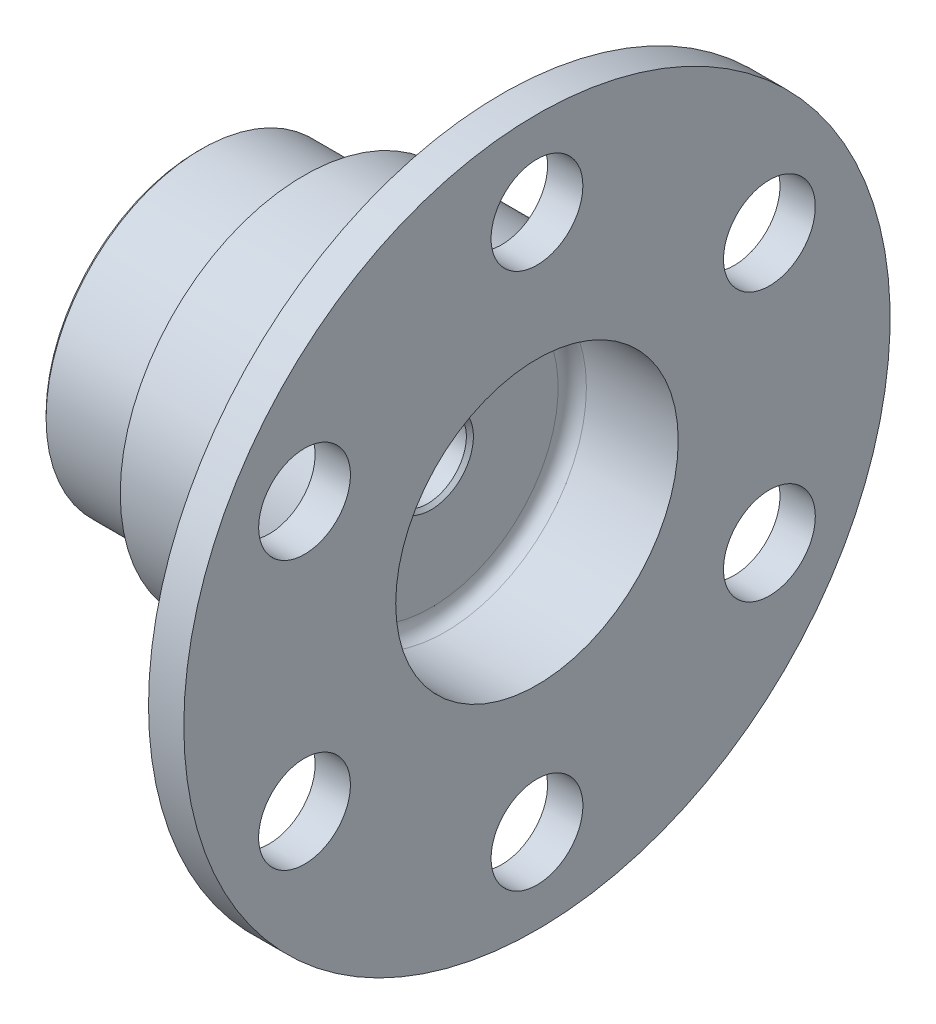
SolidWorks part; units mm, degrees
material "1.0035 (S185)"
ref_plane "Płaszczyzna przednia" through (0, 0, 0) normal (0, 0, 1) x (1, 0, 0)
ref_plane "Płaszczyzna górna" through (0, 0, 0) normal (0, 1, 0) x (1, 0, 0)
ref_plane "Płaszczyzna prawa" through (0, 0, 0) normal (1, 0, 0) x (0, 0, -1)
sketch "Szkic2" plane through (0, 0, 0) normal (0, 0, 1) x (1, 0, 0)
  line L0 (0, 0) -> (86.0541, 0) construction
  line L1 (0, 15.75) -> (29, 15.75)
  line L2 (29, 15.75) -> (29, 5.5)
  line L3 (29, 5.5) -> (33, 5.5)
  line L4 (33, 5.5) -> (33, 20)
  line L5 (33, 20) -> (48, 20)
  line L6 (48, 20) -> (48, 50)
  line L7 (48, 50) -> (43, 50)
  line L8 (43, 50) -> (43, 26)
  line L9 (43, 26) -> (15, 26)
  line L10 (0, 22) -> (0, 15.75)
  line L11 (0, 22) -> (15, 22)
  line L12 (15, 22) -> (15, 26)
  dimension "D1" = 11
  dimension "D2" = 31.5
  dimension "D3" = 5
  dimension "D4" = 4
  dimension "D5" = 29
  dimension "D6" = 100
  dimension "D7" = 52
  dimension "D8" = 15
  dimension "D9" = 40
  dimension "D10" = 15
  dimension "D11" = 44
revolve "Obrót1" add sketch "Szkic2" angle 360 about L0
sketch "Szkic4" plane through (48, 0, 0) normal (1, 0, 0) x (0, 0, -1)
  circle A0 centre (0, 38) radius 6.5
  dimension "D2" = 13
  dimension "D1" = 38
extrude "Wytnij-wyciągnięcie1" cut sketch "Szkic4" against normal blind 10
pattern_circular "Szyk kołowy1" count 6 over 360 about axis through (0, 0, 0) along (1, 0, 0) of "Wytnij-wyciągnięcie1"
fillet "Zaokrąglenie1" radius 2 2 edges at (43, 0, 26) (33, 0, 20)
sketch "Szkic6" plane through (29, 0, 0) normal (-1, 0, 0) x (0, 0, 1)
  line L0 (-4.3282, -14.981) -> (-4.3392, -15.181)
  line L1 (2.6503, -15.5649) -> (2.6612, -15.3649)
  line L2 (-12.1545, -10.0776) -> (-11.9758, -9.9872)
  line L3 (-4.1816, -15.1847) -> (-4.1926, -15.3847) construction
  line L4 (-15.138, -3.7421) -> (-15.3167, -3.8326)
  line L5 (-14.8047, 5.4873) -> (-14.637, 5.3777)
  line L6 (-10.8098, 11.2388) -> (-10.9775, 11.3483)
  line L7 (-2.6503, 15.5649) -> (-2.6612, 15.3649)
  line L8 (4.3282, 14.981) -> (4.3392, 15.181)
  line L9 (12.1545, 10.0776) -> (11.9758, 9.9872)
  line L10 (15.138, 3.7421) -> (15.3167, 3.8326)
  line L11 (14.8047, -5.4873) -> (14.637, -5.3777)
  line L12 (13.2775, 2.8001) -> (15.138, 3.7421)
  line L13 (14.637, -5.3777) -> (12.8909, -4.2376)
  line L14 (9.0637, -10.0986) -> (10.8098, -11.2388)
  line L15 (2.6612, -15.3649) -> (2.7756, -13.2826)
  line L16 (-4.2138, -12.8987) -> (-4.3282, -14.981)
  line L17 (-11.9758, -9.9872) -> (-10.1153, -9.0451)
  line L18 (-13.2775, -2.8001) -> (-15.138, -3.7421)
  line L19 (-14.637, 5.3777) -> (-12.8909, 4.2376)
  line L20 (-9.0637, 10.0986) -> (-10.8098, 11.2388)
  line L21 (-2.6612, 15.3649) -> (-2.7756, 13.2826)
  line L22 (4.2138, 12.8987) -> (4.3282, 14.981)
  line L23 (11.9758, 9.9872) -> (10.1153, 9.0451)
  line L24 (13.2775, 2.8001) -> (15.138, 3.7421)
  line L25 (14.637, -5.3777) -> (12.8909, -4.2376)
  line L26 (9.0637, -10.0986) -> (10.8098, -11.2388)
  line L27 (2.6612, -15.3649) -> (2.7756, -13.2826)
  line L28 (-4.2138, -12.8987) -> (-4.3282, -14.981)
  line L29 (-11.9758, -9.9872) -> (-10.1153, -9.0451)
  line L30 (-13.2775, -2.8001) -> (-15.138, -3.7421)
  line L31 (-14.637, 5.3777) -> (-12.8909, 4.2376)
  line L32 (-9.0637, 10.0986) -> (-10.8098, 11.2388)
  line L33 (-2.6612, 15.3649) -> (-2.7756, 13.2826)
  line L34 (4.2138, 12.8987) -> (4.3282, 14.981)
  line L35 (11.9758, 9.9872) -> (10.1153, 9.0451)
  line L36 (10.8098, -11.2388) -> (10.9775, -11.3483)
  circle A0 centre (0, 0) radius 16.5
  arc A1 (-12.4, -10.0254) -> (-12.1545, -10.0776) centre (-12.2448, -9.8992) ccw
  arc A2 (-4.3392, -15.181) -> (-4.1926, -15.3847) centre (-4.1395, -15.1919) ccw
  arc A3 (-4.1926, -15.3847) -> (2.4822, -15.7514) centre (-0.011, -0.2) ccw
  arc A4 (2.4822, -15.7514) -> (2.6503, -15.5649) centre (2.4506, -15.5539) ccw
  arc A5 (-15.4199, -4.0615) -> (-12.4, -10.0254) centre (-0.1787, -0.0905) ccw
  arc A6 (-15.3167, -3.8326) -> (-15.4199, -4.0615) centre (-15.2263, -4.011) ccw
  arc A7 (-14.8822, 5.726) -> (-14.8047, 5.4873) centre (-14.6954, 5.6547) ccw
  arc A8 (-11.2273, 11.3233) -> (-14.8822, 5.726) centre (-0.1677, 0.1095) ccw
  arc A9 (-10.9775, 11.3483) -> (-11.2273, 11.3233) centre (-11.0868, 11.1809) ccw
  arc A10 (-2.4822, 15.7514) -> (-2.6503, 15.5649) centre (-2.4506, 15.5539) ccw
  arc A11 (4.1926, 15.3847) -> (-2.4822, 15.7514) centre (0.011, 0.2) ccw
  arc A12 (4.3392, 15.181) -> (4.1926, 15.3847) centre (4.1395, 15.1919) ccw
  arc A13 (12.4, 10.0254) -> (12.1545, 10.0776) centre (12.2448, 9.8992) ccw
  arc A14 (15.4199, 4.0615) -> (12.4, 10.0254) centre (0.1787, 0.0905) ccw
  arc A15 (15.3167, 3.8326) -> (15.4199, 4.0615) centre (15.2263, 4.011) ccw
  arc A16 (14.8822, -5.726) -> (14.8047, -5.4873) centre (14.6954, -5.6547) ccw
  arc A17 (11.2273, -11.3233) -> (14.8822, -5.726) centre (0.1677, -0.1095) ccw
  arc A18 (10.9775, -11.3483) -> (11.2273, -11.3233) centre (11.0868, -11.1809) ccw
  arc A36 (12.2213, 9.9349) -> (11.9758, 9.9872) centre (12.0661, 9.8087) ccw
  arc A37 (15.2412, 3.971) -> (12.2213, 9.9349) centre (0, 0) ccw
  arc A38 (15.138, 3.7421) -> (15.2412, 3.971) centre (15.0476, 3.9206) ccw
  arc A39 (13.2775, 2.8001) -> (13.1182, 2.4768) centre (13.413, 2.5324) ccw
  arc A40 (12.768, -3.8987) -> (13.1182, 2.4768) centre (0, 0) ccw
  arc A41 (12.768, -3.8987) -> (12.8909, -4.2376) centre (13.0549, -3.9864) ccw
  arc A42 (14.7145, -5.6165) -> (14.637, -5.3777) centre (14.5277, -5.5452) ccw
  arc A43 (15.2412, 3.971) -> (12.2213, 9.9349) centre (0, 0) ccw construction
  arc A44 (10.8098, -11.2388) -> (11.0596, -11.2138) centre (10.9191, -11.0714) ccw
  arc A45 (9.0637, -10.0986) -> (8.7041, -10.1223) centre (8.8996, -10.3498) ccw
  arc A46 (3.0076, -13.0068) -> (8.7041, -10.1223) centre (0, 0) ccw
  arc A47 (3.0076, -13.0068) -> (2.7756, -13.2826) centre (3.0752, -13.2991) ccw
  arc A48 (2.4932, -15.5514) -> (2.6612, -15.3649) centre (2.4615, -15.3539) ccw
  arc A49 (11.0596, -11.2138) -> (14.7145, -5.6165) centre (0, 0) ccw
  arc A50 (-4.3282, -14.981) -> (-4.1816, -15.1847) centre (-4.1285, -14.9919) ccw
  arc A51 (-4.2138, -12.8987) -> (-4.4142, -12.5991) centre (-4.5134, -12.8822) ccw
  arc A52 (-9.7604, -9.1081) -> (-4.4142, -12.5991) centre (0, 0) ccw
  arc A53 (-9.7604, -9.1081) -> (-10.1153, -9.0451) centre (-9.9798, -9.3127) ccw
  arc A54 (-12.2213, -9.9349) -> (-11.9758, -9.9872) centre (-12.0661, -9.8087) ccw
  arc A55 (11.0596, -11.2138) -> (14.7145, -5.6165) centre (0, 0) ccw construction
  arc A56 (-15.138, -3.7421) -> (-15.2412, -3.971) centre (-15.0476, -3.9206) ccw
  arc A57 (-13.2775, -2.8001) -> (-13.1182, -2.4768) centre (-13.413, -2.5324) ccw
  arc A58 (-12.768, 3.8987) -> (-13.1182, -2.4768) centre (0, 0) ccw
  arc A59 (-12.768, 3.8987) -> (-12.8909, 4.2376) centre (-13.0549, 3.9864) ccw
  arc A60 (-14.7145, 5.6165) -> (-14.637, 5.3777) centre (-14.5277, 5.5452) ccw
  arc A61 (-4.1816, -15.1847) -> (2.4932, -15.5514) centre (0, 0) ccw
  arc A62 (-10.8098, 11.2388) -> (-11.0596, 11.2138) centre (-10.9191, 11.0714) ccw
  arc A63 (-9.0637, 10.0986) -> (-8.7041, 10.1223) centre (-8.8996, 10.3498) ccw
  arc A64 (-3.0076, 13.0068) -> (-8.7041, 10.1223) centre (0, 0) ccw
  arc A65 (-3.0076, 13.0068) -> (-2.7756, 13.2826) centre (-3.0752, 13.2991) ccw
  arc A66 (-2.4932, 15.5514) -> (-2.6612, 15.3649) centre (-2.4615, 15.3539) ccw
  arc A67 (-4.1816, -15.1847) -> (2.4932, -15.5514) centre (0, 0) ccw construction
  arc A68 (4.3282, 14.981) -> (4.1816, 15.1847) centre (4.1285, 14.9919) ccw
  arc A69 (4.2138, 12.8987) -> (4.4142, 12.5991) centre (4.5134, 12.8822) ccw
  arc A70 (9.7604, 9.1081) -> (4.4142, 12.5991) centre (0, 0) ccw
  arc A71 (9.7604, 9.1081) -> (10.1153, 9.0451) centre (9.9798, 9.3127) ccw
  arc A72 (12.2213, 9.9349) -> (11.9758, 9.9872) centre (12.0661, 9.8087) ccw construction
  arc A73 (-15.2412, -3.971) -> (-12.2213, -9.9349) centre (0, 0) ccw
  arc A74 (15.138, 3.7421) -> (15.2412, 3.971) centre (15.0476, 3.9206) ccw construction
  arc A75 (13.2775, 2.8001) -> (13.1182, 2.4768) centre (13.413, 2.5324) ccw
  arc A76 (12.768, -3.8987) -> (13.1182, 2.4768) centre (0, 0) ccw
  arc A77 (12.768, -3.8987) -> (12.8909, -4.2376) centre (13.0549, -3.9864) ccw
  arc A78 (14.7145, -5.6165) -> (14.637, -5.3777) centre (14.5277, -5.5452) ccw construction
  arc A79 (-15.2412, -3.971) -> (-12.2213, -9.9349) centre (0, 0) ccw construction
  arc A80 (10.8098, -11.2388) -> (11.0596, -11.2138) centre (10.9191, -11.0714) ccw construction
  arc A81 (9.0637, -10.0986) -> (8.7041, -10.1223) centre (8.8996, -10.3498) ccw
  arc A82 (3.0076, -13.0068) -> (8.7041, -10.1223) centre (0, 0) ccw
  arc A83 (3.0076, -13.0068) -> (2.7756, -13.2826) centre (3.0752, -13.2991) ccw
  arc A84 (2.4932, -15.5514) -> (2.6612, -15.3649) centre (2.4615, -15.3539) ccw construction
  arc A85 (-11.0596, 11.2138) -> (-14.7145, 5.6165) centre (0, 0) ccw
  arc A86 (-4.3282, -14.981) -> (-4.1816, -15.1847) centre (-4.1285, -14.9919) ccw construction
  arc A87 (-4.2138, -12.8987) -> (-4.4142, -12.5991) centre (-4.5134, -12.8822) ccw
  arc A88 (-9.7604, -9.1081) -> (-4.4142, -12.5991) centre (0, 0) ccw
  arc A89 (-9.7604, -9.1081) -> (-10.1153, -9.0451) centre (-9.9798, -9.3127) ccw
  arc A90 (-12.2213, -9.9349) -> (-11.9758, -9.9872) centre (-12.0661, -9.8087) ccw construction
  arc A91 (-11.0596, 11.2138) -> (-14.7145, 5.6165) centre (0, 0) ccw construction
  arc A92 (-15.138, -3.7421) -> (-15.2412, -3.971) centre (-15.0476, -3.9206) ccw construction
  arc A93 (-13.2775, -2.8001) -> (-13.1182, -2.4768) centre (-13.413, -2.5324) ccw
  arc A94 (-12.768, 3.8987) -> (-13.1182, -2.4768) centre (0, 0) ccw
  arc A95 (-12.768, 3.8987) -> (-12.8909, 4.2376) centre (-13.0549, 3.9864) ccw
  arc A96 (-14.7145, 5.6165) -> (-14.637, 5.3777) centre (-14.5277, 5.5452) ccw construction
  arc A97 (4.1816, 15.1847) -> (-2.4932, 15.5514) centre (0, 0) ccw
  arc A98 (-10.8098, 11.2388) -> (-11.0596, 11.2138) centre (-10.9191, 11.0714) ccw construction
  arc A99 (-9.0637, 10.0986) -> (-8.7041, 10.1223) centre (-8.8996, 10.3498) ccw
  arc A100 (-3.0076, 13.0068) -> (-8.7041, 10.1223) centre (0, 0) ccw
  arc A101 (-3.0076, 13.0068) -> (-2.7756, 13.2826) centre (-3.0752, 13.2991) ccw
  arc A102 (-2.4932, 15.5514) -> (-2.6612, 15.3649) centre (-2.4615, 15.3539) ccw construction
  arc A103 (4.1816, 15.1847) -> (-2.4932, 15.5514) centre (0, 0) ccw construction
  arc A104 (4.3282, 14.981) -> (4.1816, 15.1847) centre (4.1285, 14.9919) ccw construction
  arc A105 (4.2138, 12.8987) -> (4.4142, 12.5991) centre (4.5134, 12.8822) ccw
  arc A106 (9.7604, 9.1081) -> (4.4142, 12.5991) centre (0, 0) ccw
  arc A107 (9.7604, 9.1081) -> (10.1153, 9.0451) centre (9.9798, 9.3127) ccw
  point P140 (0, 0)
  dimension "D2" = 33
  dimension "D3" = 0.2
  dimension "D4" = 0.2
  dimension "D5" = 0.2
  dimension "D1" = 0
  dimension "D6" = 6
extrude "Dodanie-wyciągnięcie1" add sketch "Szkic6" along normal blind 26
chamfer "Sfazowanie1" distance 0.5 4 edges at (0, 0, 15.75) (29, 0, 5.5) (33, 0, 5.5) (0, 0, 22)
